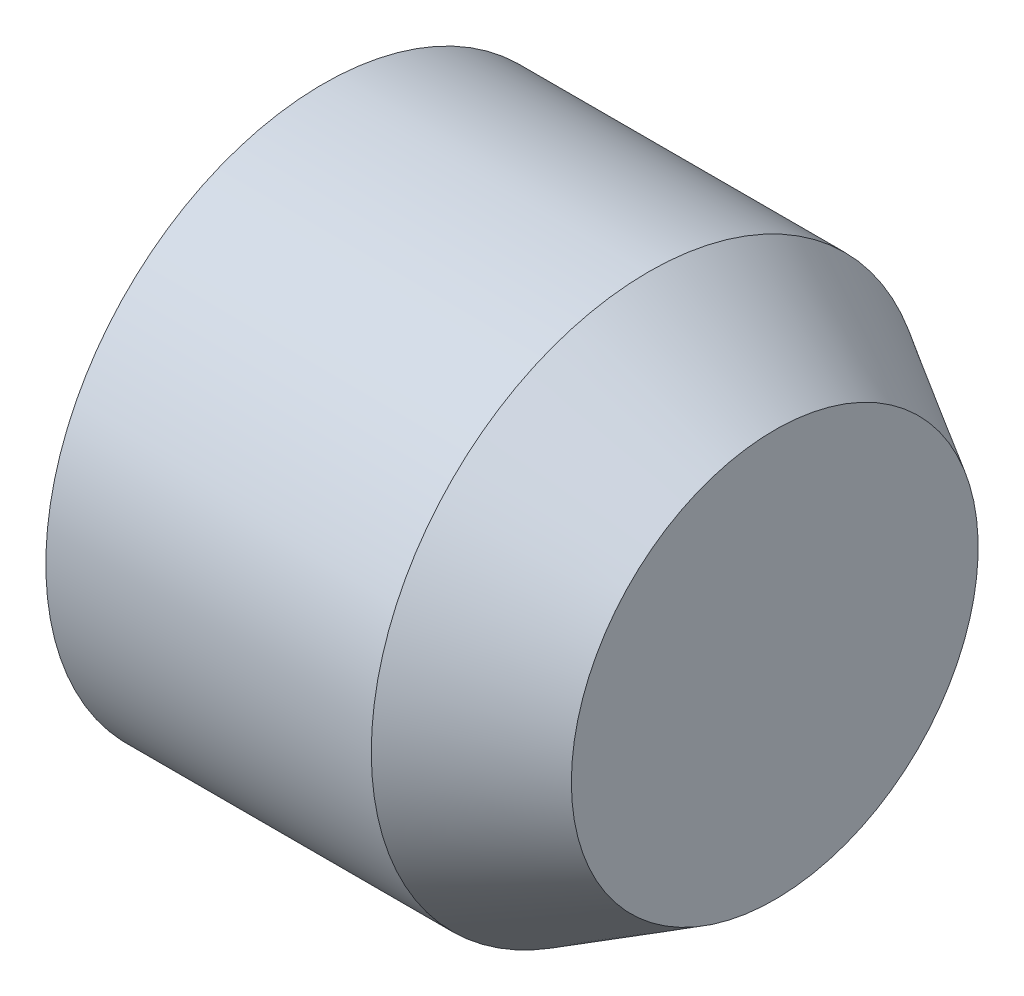
SolidWorks part; units mm, degrees
ref_plane "Front Plane" through (0, 0, 0) normal (0, 0, 1) x (1, 0, 0)
ref_plane "Top Plane" through (0, 0, 0) normal (0, 1, 0) x (1, 0, 0)
ref_plane "Right Plane" through (0, 0, 0) normal (1, 0, 0) x (0, 0, -1)
sketch "Sketch1" plane through (0, 0, 0) normal (1, 0, 0) x (0, 0, -1)
  circle A0 centre (0, 0) radius 31.69 construction
  circle A1 centre (0, 0) radius 32.09
  circle A2 centre (0, 0) radius 34.09
  dimension "D1" = 63.38
  dimension "D2" = 0.4
  dimension "D3" = 2
extrude "Boss-Extrude1" add sketch "Sketch1" along normal blind 40
sketch "Sketch2" plane through (0, 0, 0) normal (-1, 0, 0) x (0, 0, 1)
  circle A1 centre (0, 0) radius 32.09
curve "Helix/Spiral1" pitch 10 height 12.5 turns 1.25
sketch "Sketch3" plane through (0, 0, 0) normal (0, 1, 0) x (1, 0, 0)
  circle A0 centre (0, -32.09) radius 1.25
  dimension "D1" = 2.5
sweep "Sweep1" add profiles "Sketch3" path "Helix/Spiral1"
sketch "Sketch4" plane through (0, 0, 0) normal (-1, 0, 0) x (0, 0, 1)
  circle A0 centre (0, 0) radius 34.09
extrude "Cut-Extrude1" cut sketch "Sketch4" along normal through all
chamfer "Chamfer1" distance 1.2 angle 45 1 edges at (0, 0, 31.465)
sketch "Sketch5" plane through (0, 0, 0) normal (0, 1, 0) x (1, 0, 0)
  line L0 (40, 0) -> (55.5, 0) construction
  line L1 (40, -34.09) -> (40, 34.09) construction
  line L2 (55.5, 0) -> (55.5, 25)
  line L3 (55.5, 25) -> (40, 34.09)
  line L4 (40, 32.09) -> (53.5, 23)
  line L5 (53.5, 23) -> (53.5, 0)
  line L6 (53.5, 0) -> (55.5, 0)
  line L7 (40, 34.09) -> (40, 32.09)
  line L8 (59.3682, 28.8682) -> (50.9808, 20.4808) construction
  dimension "D1" = 15.5
  dimension "D2" = 25
  dimension "D3" = 2
revolve "Revolve1" add sketch "Sketch5" angle 360 about L0
